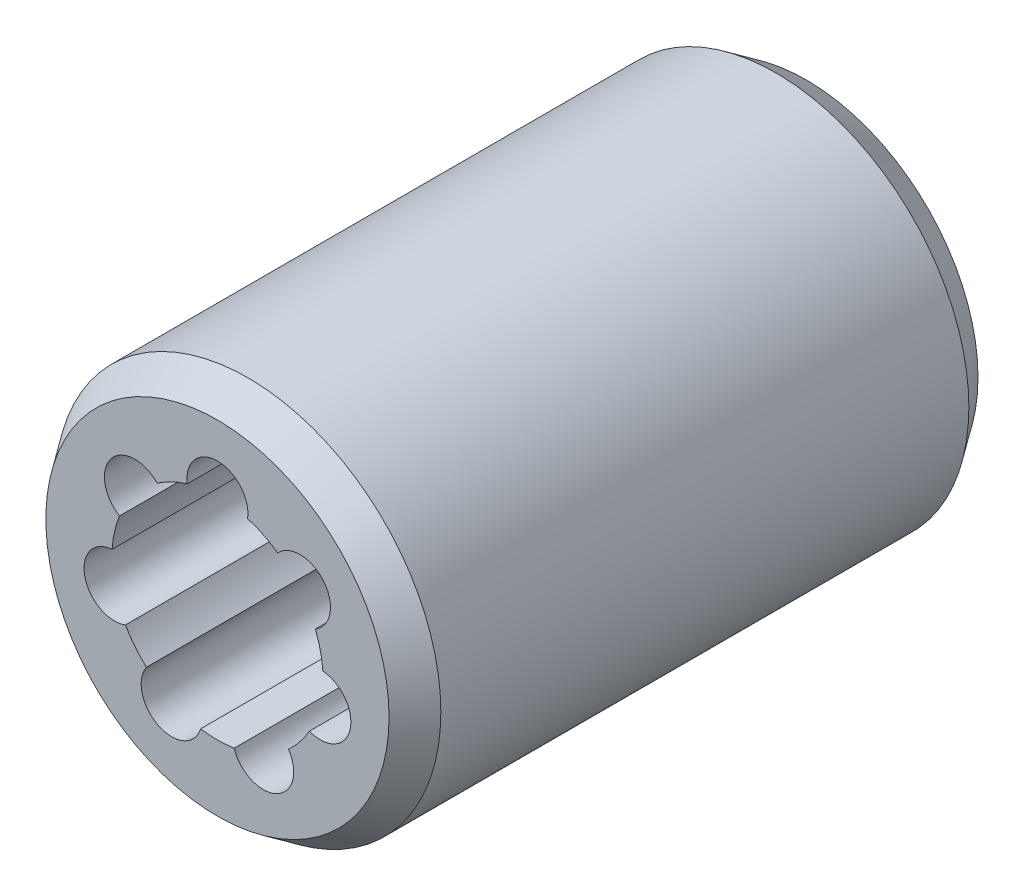
SolidWorks part; units mm, degrees
ref_plane "Front Plane" through (0, 0, 0) normal (0, 0, 1) x (1, 0, 0)
ref_plane "Top Plane" through (0, 0, 0) normal (0, 1, 0) x (1, 0, 0)
ref_plane "Right Plane" through (0, 0, 0) normal (1, 0, 0) x (0, 0, -1)
sketch "Sketch1" plane through (0, 0, 0) normal (0, 0, 1) x (1, 0, 0)
  circle A0 centre (0, 0) radius 9.5
  circle A1 centre (0, 0) radius 5.2
  dimension "D1" = 19
  dimension "D2" = 10.4
extrude "Boss-Extrude1" add sketch "Sketch1" along normal blind 29
sketch "Sketch2" plane through (0, 0, 29) normal (0, 0, 1) x (1, 0, 0)
  circle A0 centre (0, 0) radius 5.2 construction
  circle A1 centre (0, 0) radius 5.2 construction
  circle A2 centre (0, 5.2) radius 1.5
  dimension "D1" = 3
extrude "Cut-Extrude1" cut sketch "Sketch2" against normal through all
pattern_circular "CirPattern1" count 7 over 360 about axis through (0, 0, 0) along (0, 0, 1) of "Cut-Extrude1"
chamfer "Chamfer1" distance 1.5 angle 35 2 edges at (9.5, 0, 0) (9.5, 0, 29)
